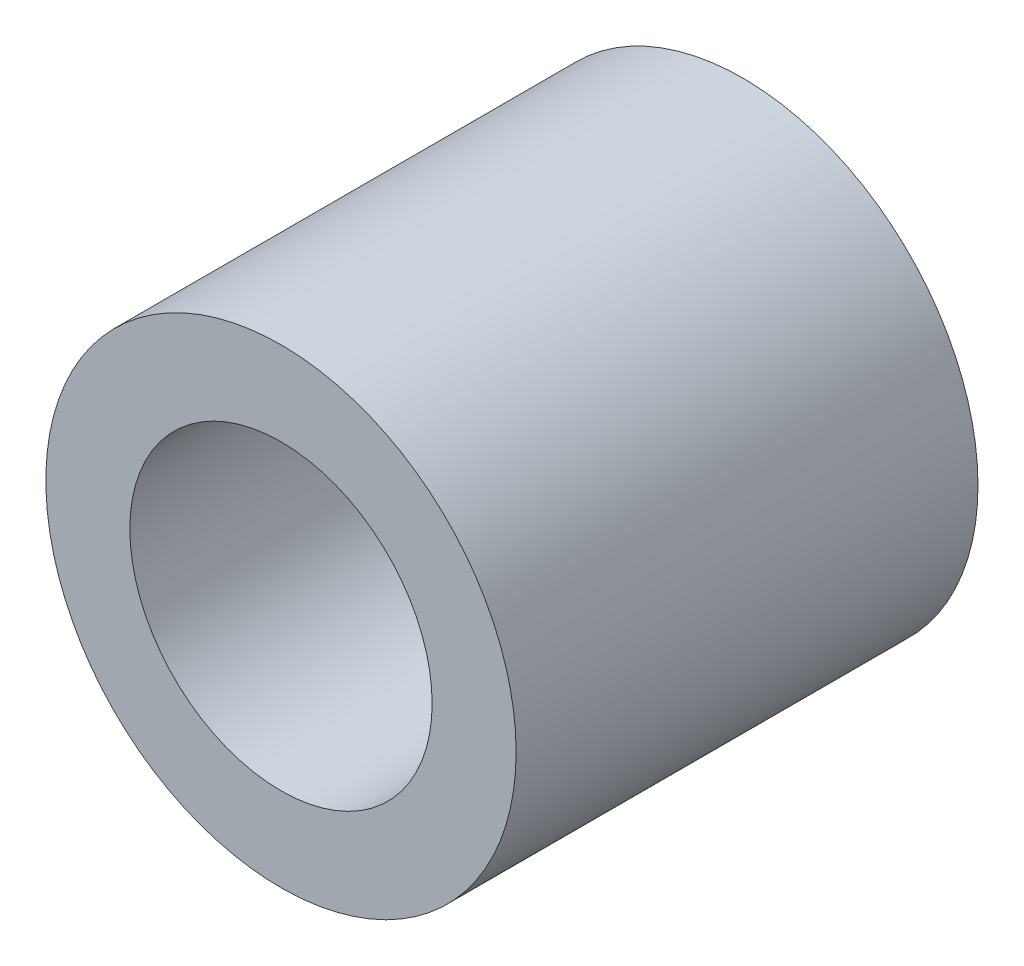
SolidWorks part; units mm, degrees
ref_plane "Front Plane" through (0, 0, 0) normal (0, 0, 1) x (1, 0, 0)
ref_plane "Top Plane" through (0, 0, 0) normal (0, 1, 0) x (1, 0, 0)
ref_plane "Right Plane" through (0, 0, 0) normal (1, 0, 0) x (0, 0, -1)
sketch "Sketch1" plane through (0, 0, 0) normal (0, 0, 1) x (1, 0, 0)
  circle A0 centre (0, 0) radius 1.8
  circle A1 centre (0, 0) radius 2.8
  dimension "D1" = 3.6
  dimension "D2" = 1
extrude "Boss-Extrude1" add sketch "Sketch1" along normal blind 5.5
